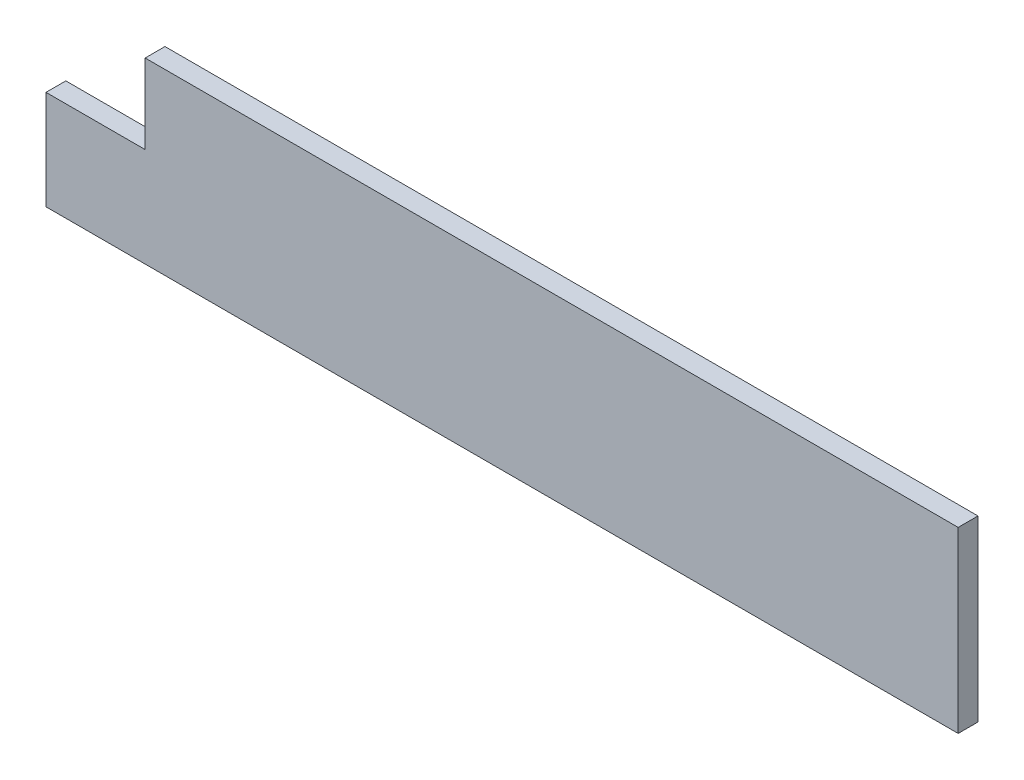
SolidWorks part; units mm, degrees
ref_plane "Front Plane" through (0, 0, 0) normal (0, 0, 1) x (1, 0, 0)
ref_plane "Top Plane" through (0, 0, 0) normal (0, 1, 0) x (1, 0, 0)
ref_plane "Right Plane" through (0, 0, 0) normal (1, 0, 0) x (0, 0, -1)
sketch "Sketch1" plane through (0, 0, 0) normal (0, 0, 1) x (1, 0, 0)
  line L1 (0, 0) -> (292.1, 0)
  line L2 (0, 0) -> (0, 57.15)
  line L3 (0, 57.15) -> (292.1, 57.15)
  line L4 (292.1, 0) -> (292.1, 57.15)
  dimension "D1" = 292.1
  dimension "D2" = 57.15
extrude "Boss-Extrude1" add sketch "Sketch1" along normal blind 6.35 contours L3 L4 L1 L2
sketch "Sketch3" plane through (0, 0, 6.35) normal (0, 0, 1) x (1, 0, 0)
  line L1 (0, 57.15) -> (31.75, 57.15)
  line L2 (0, 57.15) -> (0, 31.75)
  line L3 (0, 31.75) -> (31.75, 31.75)
  line L4 (31.75, 57.15) -> (31.75, 31.75)
  dimension "D1" = 31.75
  dimension "D2" = 25.4
extrude "Cut-Extrude2" cut sketch "Sketch3" against normal through all and the other way through all
